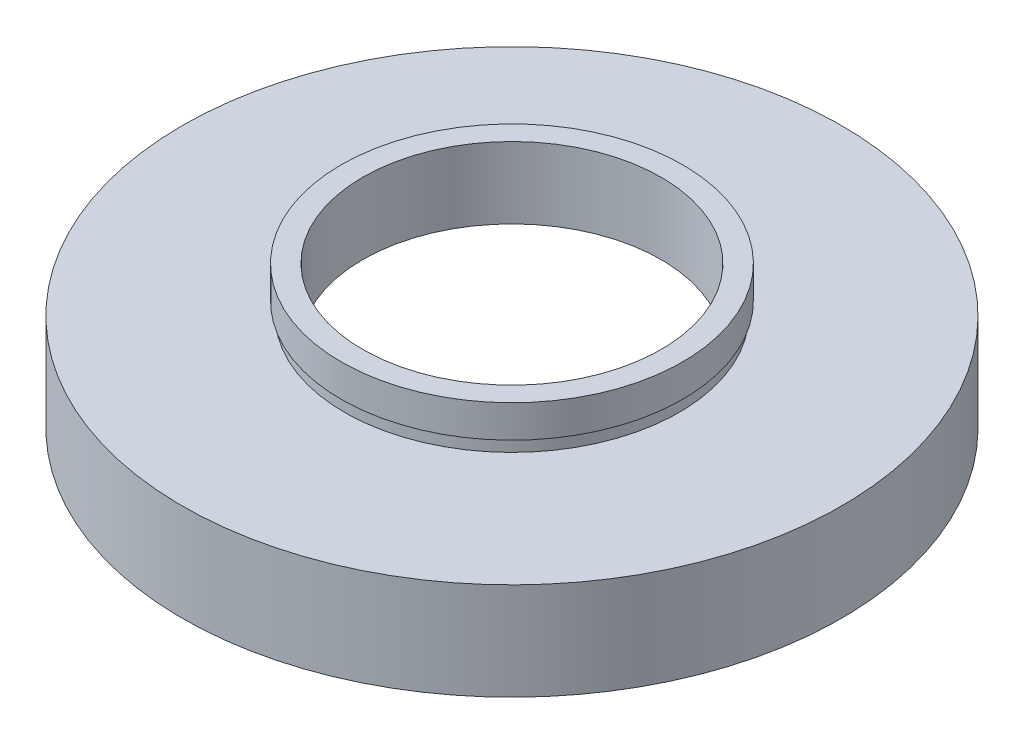
SolidWorks part; units mm, degrees
ref_plane "前视基准面" through (0, 0, 0) normal (0, 0, 1) x (1, 0, 0)
ref_plane "上视基准面" through (0, 0, 0) normal (0, 1, 0) x (1, 0, 0)
ref_plane "右视基准面" through (0, 0, 0) normal (1, 0, 0) x (0, 0, -1)
sketch "草图1" plane through (0, 0, 0) normal (0, 0, 1) x (1, 0, 0)
  line L0 (0, 16.886) -> (0, -24.4878) construction
  line L1 (23, 0) -> (23, 4.5)
  line L2 (11.5, 5.5) -> (24.1, 5.5)
  line L3 (11.5, 5.5) -> (11.5, 11)
  line L4 (11.5, 11) -> (13.16, 11)
  line L5 (13.16, 11) -> (13.16, 8.5)
  line L6 (13.16, 8.5) -> (12.9, 8.5)
  line L7 (12.9, 8.5) -> (12.9, 7.5)
  line L8 (12.9, 7.5) -> (25.4, 7.5)
  line L9 (25.4, 7.5) -> (25.4, 0)
  line L10 (25.4, 0) -> (23, 0)
  line L11 (23, 4.5) -> (24.1, 4.5)
  line L12 (24.1, 4.5) -> (24.1, 5.5)
  line L13 (0, 0) -> (3.4668, 0) construction
  point P4 (24.2, 0)
  dimension "D1" = 11.5
  dimension "D2" = 13.16
  dimension "D3" = 12.9
  dimension "D4" = 23
  dimension "D5" = 24.1
  dimension "D6" = 25.4
  dimension "D7" = 11
  dimension "D8" = 7.5
  dimension "D9" = 1
  dimension "D10" = 4.5
  dimension "D11" = 1
revolve "旋转1" add sketch "草图1" angle 360 about L0
cosmetic thread "装饰螺纹线1"
cosmetic thread "装饰螺纹线2"
cosmetic thread "装饰螺纹线3"
